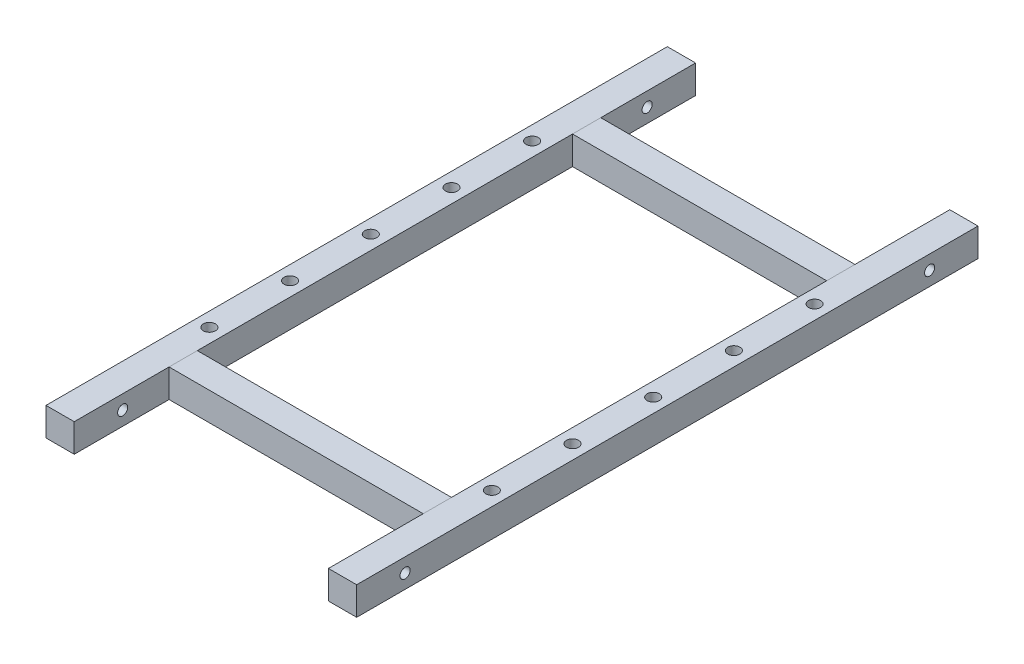
SolidWorks part; units mm, degrees
ref_plane "前视基准面" through (0, 0, 0) normal (0, 0, 1) x (1, 0, 0)
ref_plane "上视基准面" through (0, 0, 0) normal (0, 1, 0) x (1, 0, 0)
ref_plane "右视基准面" through (0, 0, 0) normal (1, 0, 0) x (0, 0, -1)
sketch "草图1" plane through (0, 0, 0) normal (0, 1, 0) x (1, 0, 0)
  line L0 (0, 59.6848) -> (0, -69.2663) construction
  line L1 (-35, 50) -> (35, 50)
  line L2 (-35, 77) -> (-35, -77)
  line L3 (-35, -50) -> (35, -50)
  line L4 (35, 77) -> (35, -77)
  line L5 (-43.3854, 0) -> (38.4144, 0) construction
  point P7 (-35, 0)
  dimension "D1" = 100
  dimension "D2" = 154
  dimension "D3" = 70
other "Bar 7X7(1)"
ref_plane "基准面1" through (-35, 0, -77) normal (0, 0, 1) x (1, 0, 0)
sketch "草图14" plane through (-35, 0, -77) normal (0, 0, 1) x (1, 0, 0)
  line L1 (-3.5, 3.5) -> (3.5, 3.5)
  line L2 (-3.5, 3.5) -> (-3.5, -3.5)
  line L3 (-3.5, -3.5) -> (3.5, -3.5)
  line L4 (3.5, 3.5) -> (3.5, -3.5)
  point P4 (0, 3.5)
  point P5 (-3.5, 0)
  point P7 (0, 0)
  dimension "D1" = 7
sketch "草图12" plane through (-38.5, 0, 25) normal (1, 0, 0) x (0, 0, -1)
  line L1 (102, 0) -> (-52, 0) construction
  circle A0 centre (90, 0) radius 1.25
  dimension "D1" = 65
  dimension "D2" = 2.5
extrude "切除-拉伸1" cut sketch "草图12" along normal through all
mirror "镜向1" about plane through (0, 0, 0) normal (0, 0, 1) of "切除-拉伸1"
hole_wizard "大小mm Transitional 暗销孔1" positions "草图15" profile "草图16" hole size "Ø3.0" standard "GB" end condition through all
sketch "草图15" plane through (0, 3.5, 0) normal (0, 1, 0) x (1, 0, 0)
  line L0 (47.69, 0) -> (-50.0789, 0) construction
  line L2 (-38.5, -77) -> (-38.5, 77) construction
  line L3 (0, -17.5284) -> (0, 20.3823) construction
  point P0 (-35, 0)
  point P43 (-35, 20)
  point P44 (-35, 40)
  point P45 (-35, -40)
  point P46 (-35, -20)
  point P47 (35, -20)
  point P48 (35, -40)
  point P49 (35, 40)
  point P50 (35, 20)
  point P51 (35, 0)
  dimension "D1" = 3.5
  dimension "D2" = 3
sketch "草图16" plane through (-35, 3.5, 0) normal (1, 0, 0) x (0, 0, 1)
  line L0 (0, 0) -> (0, 7)
  line L1 (0, 7) -> (1.5, 7)
  line L2 (1.5, 7) -> (1.5, 0)
  line L5 (1.5, 0) -> (0, 0)
  line L11 (0, -6.35) -> (0, 107.95) construction
  dimension "通孔孔直径" = 3
  dimension "通孔孔深度" = 7
